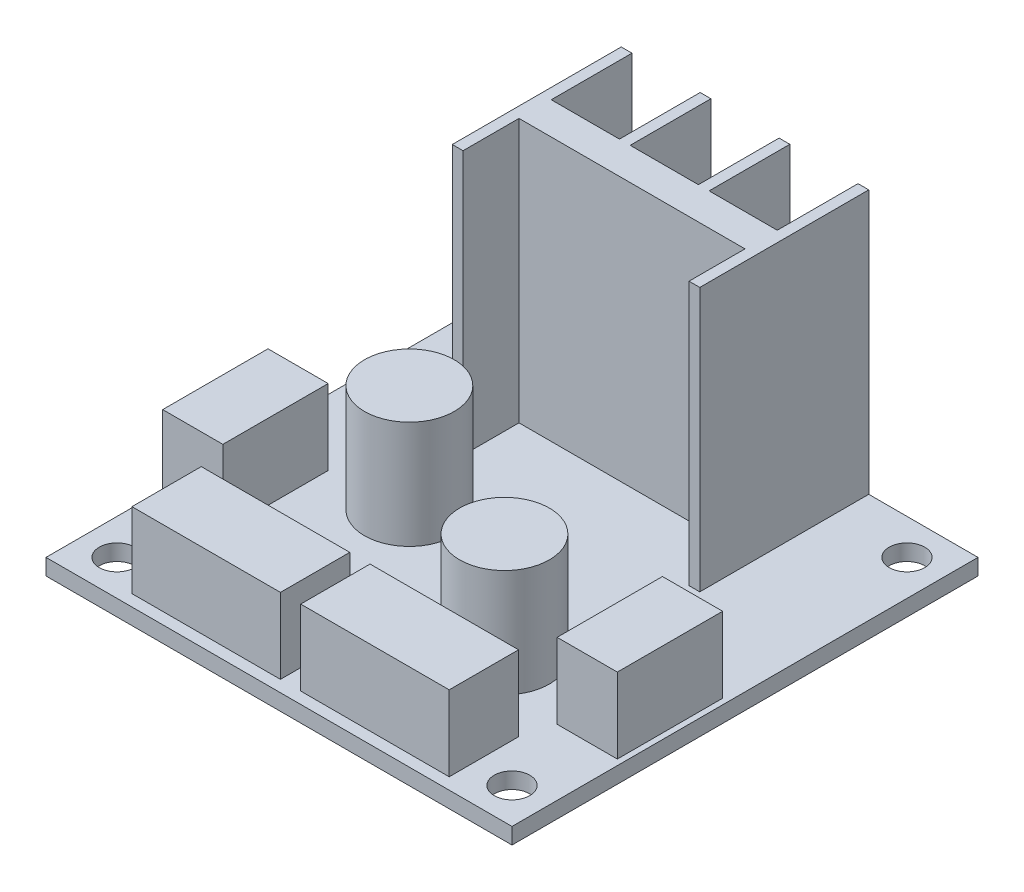
SolidWorks part; units mm, degrees
ref_plane "Front Plane" through (0, 0, 0) normal (0, 0, 1) x (1, 0, 0)
ref_plane "Top Plane" through (0, 0, 0) normal (0, 1, 0) x (1, 0, 0)
ref_plane "Right Plane" through (0, 0, 0) normal (1, 0, 0) x (0, 0, -1)
sketch "Sketch1" plane through (0, 0, 0) normal (0, 1, 0) x (1, 0, 0)
  line L1 (18.35, -18.35) -> (-18.35, -18.35) construction
  line L2 (18.35, -18.35) -> (18.35, 18.35) construction
  line L3 (18.35, 18.35) -> (-18.35, 18.35) construction
  line L4 (-18.35, -18.35) -> (-18.35, 18.35) construction
  line L5 (18.35, -18.35) -> (-18.35, 18.35) construction
  line L6 (18.35, 18.35) -> (-18.35, -18.35) construction
  line L7 (21.65, -21.65) -> (-21.65, -21.65)
  line L8 (21.65, -21.65) -> (21.65, 21.65)
  line L9 (21.65, 21.65) -> (-21.65, 21.65)
  line L10 (-21.65, -21.65) -> (-21.65, 21.65)
  line L11 (21.65, -21.65) -> (-21.65, 21.65) construction
  line L12 (21.65, 21.65) -> (-21.65, -21.65) construction
  circle A0 centre (-18.35, 18.35) radius 1.65
  circle A1 centre (18.35, 18.35) radius 1.65
  circle A2 centre (-18.35, -18.35) radius 1.65
  circle A3 centre (18.35, -18.35) radius 1.65
  point P0 (0, 0)
  point P6 (0, 0)
  dimension "D3" = 3.3
  dimension "D1" = 43.3
  dimension "D2" = 36.7
extrude "Boss-Extrude1" add sketch "Sketch1" along normal blind 1.5
sketch "Sketch2" plane through (0, 1.5, 0) normal (0, 1, 0) x (1, 0, 0)
  line L0 (21.65, 21.65) -> (-21.65, 21.65) construction
  line L1 (11.5, 5.95) -> (-11.5, 5.95)
  line L2 (11.5, 5.95) -> (11.5, 21.65)
  line L3 (11.5, 21.65) -> (-11.5, 21.65)
  line L4 (-11.5, 5.95) -> (-11.5, 21.65)
  line L5 (11.5, 5.95) -> (-11.5, 21.65) construction
  line L6 (11.5, 21.65) -> (-11.5, 5.95) construction
  line L7 (0, 13.8) -> (0, 0) construction
  point P0 (0, 13.8)
  dimension "D1" = 23
  dimension "D2" = 15.7
extrude "Boss-Extrude2" add sketch "Sketch2" along normal blind 24.5
sketch "Sketch3" plane through (0, 1.5, 0) normal (0, 1, 0) x (1, 0, 0)
  line L1 (-21.1217, -11.3358) -> (-15.5298, -11.3358)
  line L2 (-21.1217, -11.3358) -> (-21.1217, -1.5499)
  line L3 (-21.1217, -1.5499) -> (-15.5298, -1.5499)
  line L4 (-15.5298, -11.3358) -> (-15.5298, -1.5499)
  line L5 (-21.1217, -11.3358) -> (-15.5298, -1.5499) construction
  line L6 (-21.1217, -1.5499) -> (-15.5298, -11.3358) construction
  line L7 (-14.7396, -20.5747) -> (-0.9421, -20.5747)
  line L8 (-14.7396, -20.5747) -> (-14.7396, -14.1318)
  line L9 (-14.7396, -14.1318) -> (-0.9421, -14.1318)
  line L10 (-0.9421, -20.5747) -> (-0.9421, -14.1318)
  line L11 (-14.7396, -20.5747) -> (-0.9421, -14.1318) construction
  line L12 (-14.7396, -14.1318) -> (-0.9421, -20.5747) construction
  point P0 (-18.3258, -6.4429)
  point P6 (-7.8409, -17.3533)
extrude "Boss-Extrude3" add sketch "Sketch3" along normal blind 7
mirror "Mirror1" about plane through (0, 0, 0) normal (1, 0, 0) of "Boss-Extrude3"
sketch "Sketch4" plane through (0, 1.5, 0) normal (0, 1, 0) x (1, 0, 0)
  circle A0 centre (-8.5928, -0.9433) radius 4.1684
  circle A1 centre (7.7658, -8.4636) radius 4.1684
extrude "Boss-Extrude4" add sketch "Sketch4" along normal blind 10
sketch "Sketch5" plane through (0, 26, 0) normal (0, 1, 0) x (1, 0, 0)
  line L5 (-11.5, 5.95) -> (11.5, 5.95) construction
  line L6 (-10.5, 5.95) -> (10.5, 5.95)
  line L7 (11.5, 21.65) -> (-11.5, 21.65) construction
  line L8 (-3.1667, 29.15) -> (3.1667, 29.15)
  line L9 (-3.1667, 29.15) -> (-3.1667, 14.15)
  line L10 (-3.1667, 14.15) -> (3.1667, 14.15)
  line L11 (3.1667, 29.15) -> (3.1667, 14.15)
  line L12 (-3.1667, 29.15) -> (3.1667, 14.15) construction
  line L13 (-3.1667, 14.15) -> (3.1667, 29.15) construction
  line L14 (-7.3333, 21.65) -> (0, 21.65) construction
  line L15 (4.1667, 29.15) -> (10.5, 29.15)
  line L16 (4.1667, 29.15) -> (4.1667, 14.15)
  line L17 (4.1667, 14.15) -> (10.5, 14.15)
  line L18 (10.5, 29.15) -> (10.5, 14.15)
  line L19 (4.1667, 29.15) -> (10.5, 14.15) construction
  line L20 (4.1667, 14.15) -> (10.5, 29.15) construction
  line L21 (-10.5, 29.15) -> (-4.1667, 29.15)
  line L22 (-10.5, 29.15) -> (-10.5, 14.15)
  line L23 (-10.5, 14.15) -> (-4.1667, 14.15)
  line L24 (-4.1667, 29.15) -> (-4.1667, 14.15)
  line L25 (-10.5, 29.15) -> (-4.1667, 14.15) construction
  line L26 (-10.5, 14.15) -> (-4.1667, 29.15) construction
  line L27 (0, 21.65) -> (7.3333, 21.65) construction
  line L28 (-10.5, 5.95) -> (-10.5, 11.15)
  line L29 (-10.5, 11.15) -> (10.5, 11.15)
  line L30 (10.5, 5.95) -> (10.5, 11.15)
  line L31 (-11.5, 21.65) -> (-11.5, 5.95) construction
  line L32 (11.5, 5.95) -> (11.5, 21.65) construction
  point P7 (0, 21.65)
  point P14 (7.3333, 21.65)
  point P19 (-7.3333, 21.65)
  dimension "D1" = 1
  dimension "D2" = 1
  dimension "D3" = 15
  dimension "D4" = 1
  dimension "D5" = 3
extrude "Cut-Extrude1" cut sketch "Sketch5" against normal up to surface (24.5 mm away) up to face at (7.7658, 1.5, 12.632)
